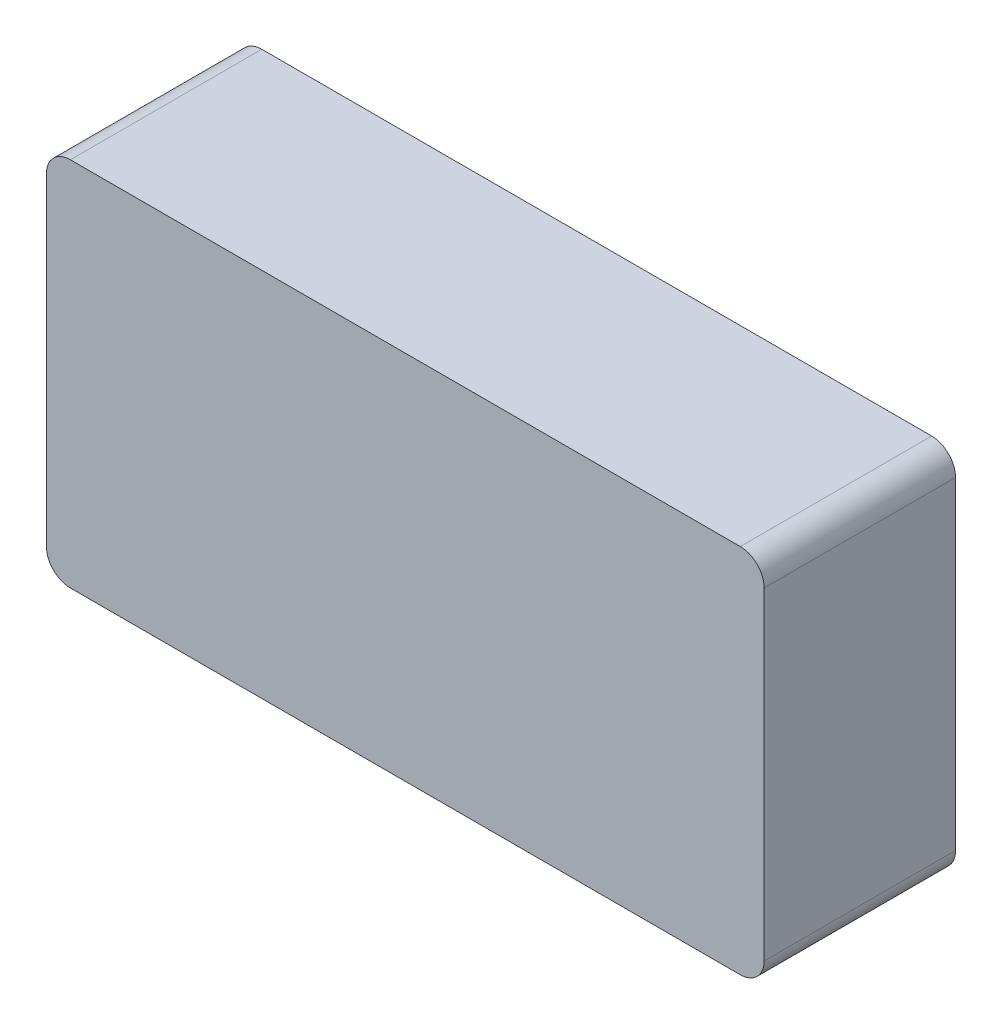
SolidWorks part; units mm, degrees
ref_plane "Plano frontal" through (0, 0, 0) normal (0, 0, 1) x (1, 0, 0)
ref_plane "Plano superior" through (0, 0, 0) normal (0, 1, 0) x (1, 0, 0)
ref_plane "Plano direito" through (0, 0, 0) normal (1, 0, 0) x (0, 0, -1)
sketch "Esboço1" plane through (0, 0, 0) normal (0, 0, 1) x (1, 0, 0)
  line L1 (0, 0) -> (60, 0)
  line L2 (0, 0) -> (0, -31)
  line L3 (0, -31) -> (60, -31)
  line L4 (60, 0) -> (60, -31)
  dimension "D1" = 31
  dimension "36" = 60
extrude "Ressalto-extrusão1" add sketch "Esboço1" along normal blind 16
fillet "Filete1" radius 2 4 edges at (60, -31, 8) (0, -31, 8) (0, 0, 8) (60, 0, 8)
